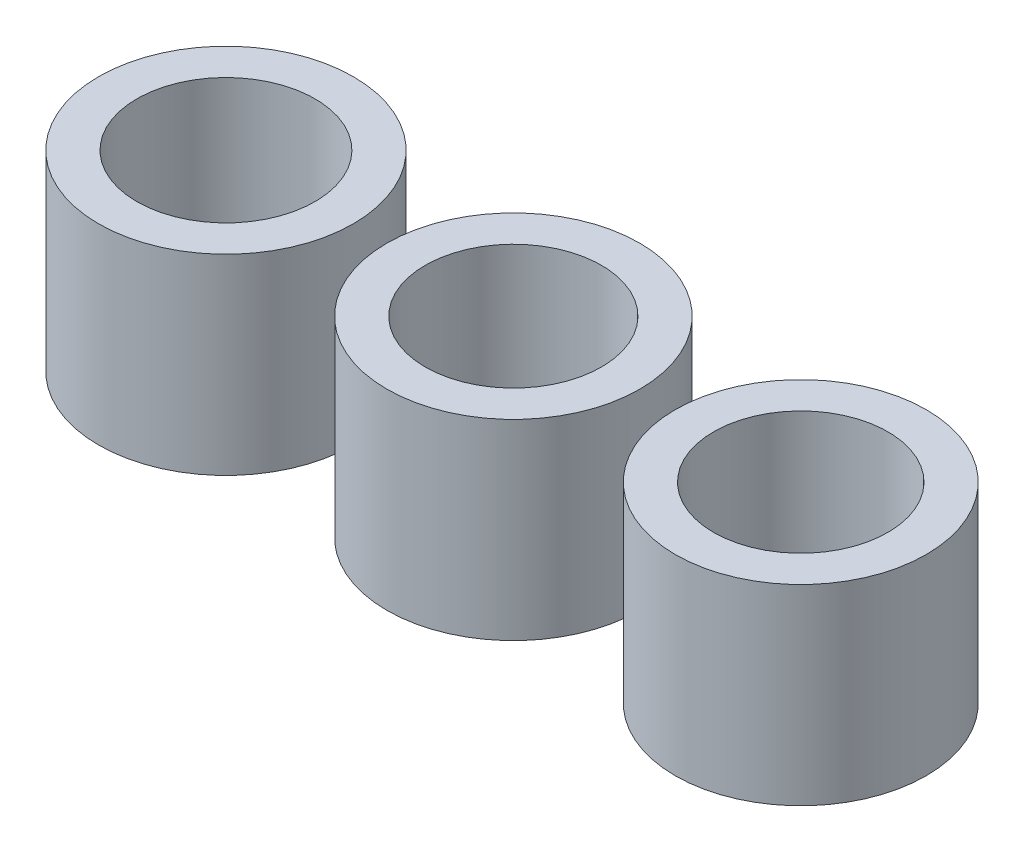
SolidWorks part; units mm, degrees
ref_plane "Front Plane" through (0, 0, 0) normal (0, 0, 1) x (1, 0, 0)
ref_plane "Top Plane" through (0, 0, 0) normal (0, 1, 0) x (1, 0, 0)
ref_plane "Right Plane" through (0, 0, 0) normal (1, 0, 0) x (0, 0, -1)
sketch "Sketch1" plane through (0, 0, 0) normal (0, 1, 0) x (1, 0, 0)
  circle A0 centre (0, 0) radius 4.65
  circle A1 centre (0, 0) radius 6.65
  circle A2 centre (15, 0) radius 4.6
  circle A3 centre (15, 0) radius 6.6
  circle A4 centre (30, 0) radius 4.55
  circle A5 centre (30, 0) radius 6.55
  dimension "D1" = 9.3
  dimension "D3" = 9.2
  dimension "D5" = 9.1
  dimension "D7" = 15
  dimension "D8" = 15
  dimension "D2" = 2
  dimension "D4" = 2
  dimension "D6" = 2
extrude "Boss-Extrude1" add sketch "Sketch1" along normal blind 10
